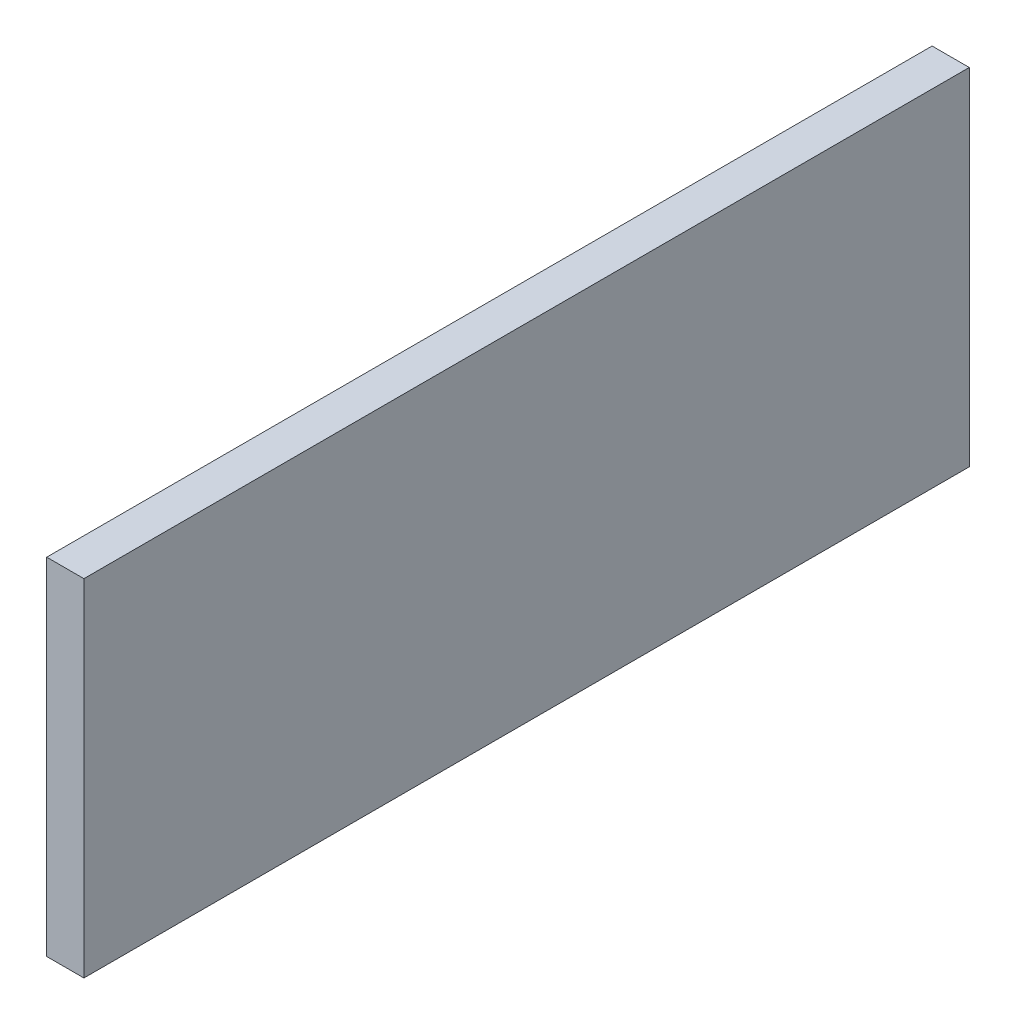
SolidWorks part; units mm, degrees
material "Maple"
ref_plane "Front Plane" through (0, 0, 0) normal (0, 0, 1) x (1, 0, 0)
ref_plane "Top Plane" through (0, 0, 0) normal (0, 1, 0) x (1, 0, 0)
ref_plane "Right Plane" through (0, 0, 0) normal (1, 0, 0) x (0, 0, -1)
sketch "Sketch1" plane through (0, 0, 0) normal (0, 0, 1) x (1, 0, 0)
  line L1 (-1.5875, 14.76) -> (1.5875, 14.76)
  line L2 (-1.5875, 14.76) -> (-1.5875, -14.76)
  line L3 (-1.5875, -14.76) -> (1.5875, -14.76)
  line L4 (1.5875, 14.76) -> (1.5875, -14.76)
  line L5 (-1.5875, 14.76) -> (1.5875, -14.76) construction
  line L6 (-1.5875, -14.76) -> (1.5875, 14.76) construction
  point P0 (0, 0)
  dimension "D1" = 3.175
  dimension "D2" = 29.52
extrude "Boss-Extrude1" add sketch "Sketch1" along normal blind 75.57
equation "\"kerf\"= 0.17 / 2"
equation "\"D2@Sketch1\"=29.35mm + 2*\"kerf\""
equation "\"D1@Boss-Extrude1\"= 75.40mm + 2*\"kerf\""
